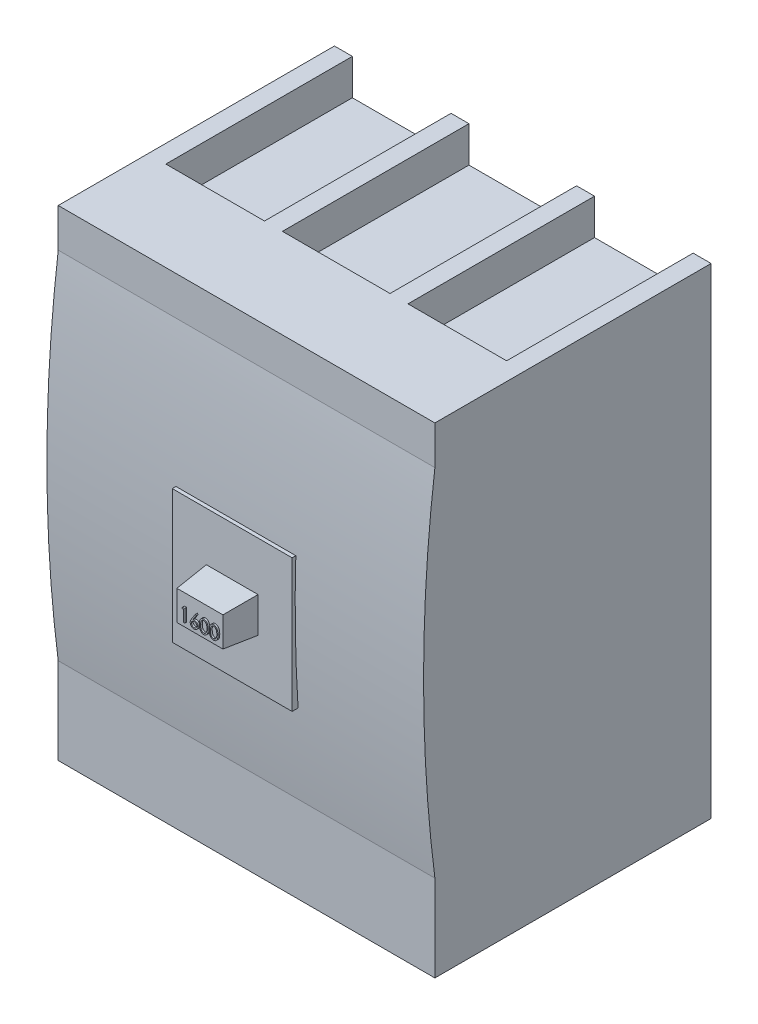
SolidWorks part; units mm, degrees
ref_plane "Alzado" through (0, 0, 0) normal (0, 0, 1) x (1, 0, 0)
ref_plane "Planta" through (0, 0, 0) normal (0, 1, 0) x (1, 0, 0)
ref_plane "Vista lateral" through (0, 0, 0) normal (1, 0, 0) x (0, 0, -1)
sketch "Croquis1" plane through (0, 0, 0) normal (0, 0, 1) x (1, 0, 0)
  line L1 (-105, -134) -> (105, -134)
  line L2 (-105, -134) -> (-105, 134)
  line L3 (-105, 134) -> (105, 134)
  line L4 (105, -134) -> (105, 134)
  line L5 (-105, -134) -> (105, 134) construction
  line L6 (-105, 134) -> (105, -134) construction
  point P0 (0, 0)
  dimension "D1" = 268
  dimension "D2" = 210
extrude "Saliente-Extruir1" add sketch "Croquis1" along normal blind 154
sketch "Croquis8" plane through (105, 0, 0) normal (1, 0, 0) x (0, 0, -1)
  line L0 (-154, -134) -> (-154, 134) construction
  line L1 (-154, -85.8093) -> (-154, 112.43)
  arc A0 (-154, -85.8093) -> (-154, 112.43) centre (620.9663, 13.3104) cw
extrude "Saliente-Extruir5" add sketch "Croquis8" against normal up to surface (210 mm away) up to face at (-105, 0, 77)
sketch "Croquis9" plane through (0, 0, 154) normal (0, 0, 1) x (1, 0, 0)
  line L1 (33.4175, 37.0991) -> (-33.4175, 37.0991)
  line L2 (33.4175, 37.0991) -> (33.4175, -37.0991)
  line L3 (33.4175, -37.0991) -> (-33.4175, -37.0991)
  line L4 (-33.4175, 37.0991) -> (-33.4175, -37.0991)
  line L5 (33.4175, 37.0991) -> (-33.4175, -37.0991) construction
  line L6 (33.4175, -37.0991) -> (-33.4175, 37.0991) construction
  point P0 (0, 0)
extrude "Saliente-Extruir6" add sketch "Croquis9" along normal blind 8
sketch "Croquis10" plane through (0, 0, 162) normal (0, 0, 1) x (1, 0, 0)
  line L1 (14.4067, 9.8361) -> (-14.4067, 9.8361)
  line L2 (14.4067, 9.8361) -> (14.4067, -9.8361)
  line L3 (14.4067, -9.8361) -> (-14.4067, -9.8361)
  line L4 (-14.4067, 9.8361) -> (-14.4067, -9.8361)
  line L5 (14.4067, 9.8361) -> (-14.4067, -9.8361) construction
  line L6 (14.4067, -9.8361) -> (-14.4067, 9.8361) construction
  point P0 (0, 0)
extrude "Saliente-Extruir7" add sketch "Croquis10" along normal blind 18 draft 5
sketch "Croquis11" plane through (0, -134, 0) normal (0, -1, 0) x (1, 0, 0)
  line L0 (35, 0) -> (35, 97.4181) construction
  line L1 (-105, 0) -> (105, 0) construction
  line L2 (105, 154) -> (105, 0) construction
  line L3 (-35, 0) -> (-35, 97.4181) construction
  line L4 (95, 0) -> (95, 104)
  line L5 (95, 104) -> (40, 104)
  line L6 (40, 104) -> (40, 0)
  line L7 (40, 0) -> (95, 0)
  line L8 (-105, 154) -> (105, 154) construction
  line L9 (30, 0) -> (30, 104)
  line L10 (30, 104) -> (-30, 104)
  line L11 (-30, 104) -> (-30, 0)
  line L12 (-30, 0) -> (30, 0)
  line L13 (-40, 0) -> (-40, 104)
  line L14 (-40, 104) -> (-100, 104)
  line L15 (-100, 104) -> (-100, 0)
  line L16 (-100, 0) -> (-40, 0)
  line L17 (-105, 154) -> (-105, 0) construction
  dimension "D1" = 70
  dimension "D2" = 70
  dimension "D3" = 50
  dimension "D4" = 10
  dimension "D5" = 5
  dimension "D6" = 5
  dimension "D7" = 5
  dimension "D8" = 5
  dimension "D9" = 5
extrude "Cortar-Extruir3" cut sketch "Croquis11" against normal blind 20
sketch "Croquis12" plane through (0, 134, 0) normal (0, 1, 0) x (1, 0, 0)
  line L0 (-35, 0) -> (-35, -95.8778) construction
  line L1 (105, 0) -> (-105, 0) construction
  line L2 (-105, -154) -> (-105, 0) construction
  line L3 (35, 0) -> (35, -95.8778) construction
  line L4 (-95, -104) -> (-95, 0)
  line L5 (-95, -104) -> (-40, -104)
  line L6 (-40, -104) -> (-40, 0)
  line L7 (-40, 0) -> (-95, 0)
  line L8 (105, -154) -> (-105, -154) construction
  line L9 (-30, 0) -> (-30, -104)
  line L10 (-30, -104) -> (28.7314, -104)
  line L11 (30, -104) -> (30, 0)
  line L12 (30, 0) -> (-30, 0)
  line L13 (28.7314, -104) -> (30, -104)
  line L14 (40, 0) -> (40, -104)
  line L15 (40, -104) -> (95, -104)
  line L16 (95, -104) -> (95, 0)
  line L17 (95, 0) -> (40, 0)
  line L18 (105, -154) -> (105, 0) construction
  dimension "D1" = 70
  dimension "D2" = 70
  dimension "D3" = 50
  dimension "D4" = 10
  dimension "D5" = 5
  dimension "D6" = 5
  dimension "D7" = 5
  dimension "D8" = 10
  dimension "D9" = 5
extrude "Cortar-Extruir4" cut sketch "Croquis12" against normal blind 20
sketch "Croquis13" plane through (0, 0, 180) normal (0, 0, 1) x (1, 0, 0)
  line L0 (-10.5498, -5.4379) -> (11.8528, -5.4379) construction
  text T0 "1600" font "Century Gothic" height in points 27
extrude "Saliente-Extruir8" add sketch "Croquis13" along normal blind 1
sketch "Croquis14" plane through (0, 0, 0) normal (0, 0, -1) x (-1, 0, 0)
  line L0 (105, 45.1013) -> (-105, 45.1013) construction
  line L1 (105, -85.8093) -> (105, 112.43) construction
  line L2 (-105, 112.43) -> (-105, -85.8093) construction
  text T0 "1600" font "Century Gothic" height in points 250
